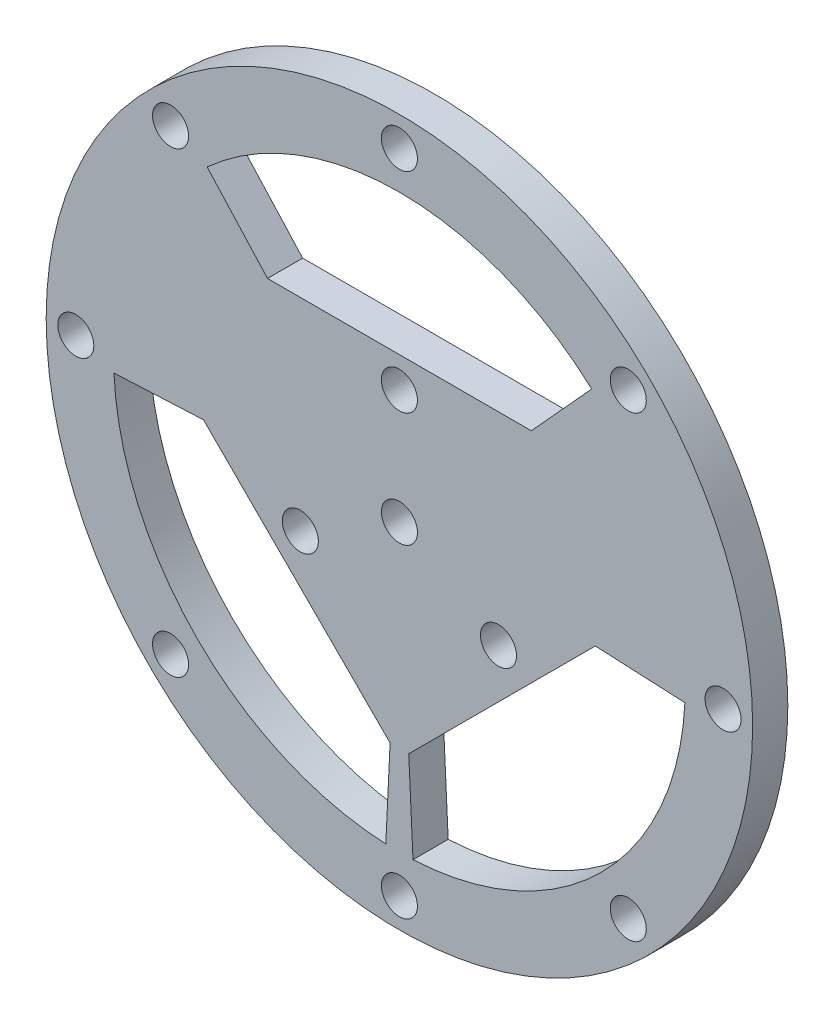
SolidWorks part; units mm, degrees
ref_plane "前视基准面" through (0, 0, 0) normal (0, 0, 1) x (1, 0, 0)
ref_plane "上视基准面" through (0, 0, 0) normal (0, 1, 0) x (1, 0, 0)
ref_plane "右视基准面" through (0, 0, 0) normal (1, 0, 0) x (0, 0, -1)
other "Configuration Table"
sketch "草图1" plane through (0, 0, 0) normal (0, 0, 1) x (1, 0, 0)
  line L0 (0, 0) -> (0, 73.6027)
  line L1 (0, 73.6027) -> (-52.0449, 52.0449)
  line L2 (-52.0449, 52.0449) -> (-73.6027, 0)
  line L3 (-73.6027, 0) -> (-52.0449, -52.0449)
  line L4 (-52.0449, -52.0449) -> (0, -73.6027)
  line L5 (0, -73.6027) -> (52.0449, -52.0449)
  line L6 (52.0449, -52.0449) -> (73.6027, 0)
  line L7 (73.6027, 0) -> (52.0449, 52.0449)
  line L8 (52.0449, 52.0449) -> (0, 73.6027)
  line L9 (43.7237, 48.0961) -> (30, 33)
  line L10 (30, 33) -> (-30, 33)
  line L11 (-43.7237, 48.0961) -> (-30, 33)
  line L12 (0, 0) -> (62.8238, 26.0225)
  line L16 (0, 0) -> (-62.8238, 26.0225)
  line L17 (0, 0) -> (0, -73.6027)
  line L18 (-64.9264, -3.0917) -> (-44.5477, -2.1213)
  line L19 (-2.1213, -44.5477) -> (-44.5477, -2.1213)
  line L20 (-3.0917, -64.9264) -> (-2.1213, -44.5477)
  line L21 (3.0917, -64.9264) -> (2.1213, -44.5477)
  line L22 (2.1213, -44.5477) -> (44.5477, -2.1213)
  line L23 (64.9264, -3.0917) -> (44.5477, -2.1213)
  line L25 (0, 26.0225) -> (-22.5361, -13.0112)
  line L26 (-22.5361, -13.0112) -> (22.5361, -13.0112)
  line L27 (22.5361, -13.0112) -> (0, 26.0225)
  circle A0 centre (0, 0) radius 80.3371
  circle A1 centre (0, 0) radius 68 construction
  circle A2 centre (0, 73.6027) radius 4.1
  circle A3 centre (-52.0449, 52.0449) radius 4.1
  circle A4 centre (-73.6027, 0) radius 4.1
  circle A5 centre (-52.0449, -52.0449) radius 4.1
  circle A6 centre (0, -73.6027) radius 4.1
  circle A7 centre (52.0449, -52.0449) radius 4.1
  circle A8 centre (73.6027, 0) radius 4.1
  circle A9 centre (52.0449, 52.0449) radius 4.1
  arc A10 (-43.7237, 48.0961) -> (43.7237, 48.0961) centre (0, 0) cw
  arc A11 (-64.9264, -3.0917) -> (-3.0917, -64.9264) centre (0, 0) ccw
  arc A12 (64.9264, -3.0917) -> (3.0917, -64.9264) centre (0, 0) cw
  circle A13 centre (0, 0) radius 13.0112 construction
  circle A14 centre (0, 26.0225) radius 4.1
  circle A15 centre (22.5361, -13.0112) radius 4.1
  circle A16 centre (-22.5361, -13.0112) radius 4.1
  circle A17 centre (0, 0) radius 4.1
  point P26 (0, 33)
  dimension "D1" = 68
  dimension "D2" = 33
  dimension "D4" = 65
  dimension "D3" = 30
extrude "凸台-拉伸1" add sketch "草图1" along normal blind 8 contours A14 L0 L10 L11 A10 A2 L1 A3 L2 L16 L25 | A14 L27 L12 L7 A9 L8 A2 L0 A10 L9 L10 | A15 L26 L17 A6 L5 A7 L6 A8 L7 L12 L27 L23 A12 L21 L22 | A16 L25 L16 L2 A4 L3 A5 L4 A6 L17 L26 A11 L18 L19 L20 | A0 A9 L7 A8 L6 A7 L5 A6 L4 A5 L3 A4 L2 A3 L1 A2 L8 | A16 L26 L17 L16 L25 | A15 L27 L12 L17 L26 | A14 L25 L16 L0 | A14 L0 L12 L27
